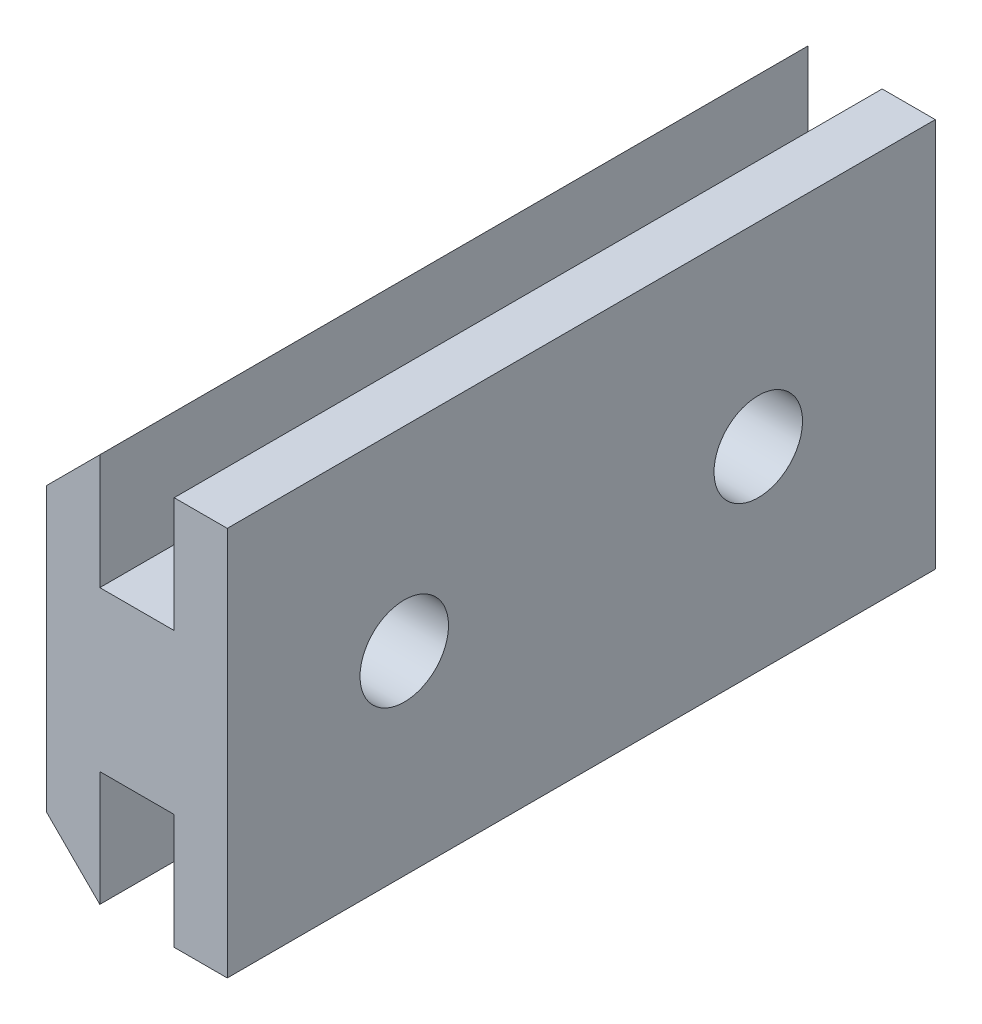
SolidWorks part; units mm, degrees
ref_plane "Plan de face" through (0, 0, 0) normal (0, 0, 1) x (1, 0, 0)
ref_plane "Plan de dessus" through (0, 0, 0) normal (0, 1, 0) x (1, 0, 0)
ref_plane "Plan de droite" through (0, 0, 0) normal (1, 0, 0) x (0, 0, -1)
sketch "ProfileRainureEsquisse" plane through (0, 0, 0) normal (0, 0, 1) x (1, 0, 0)
  line L0 (0.1, -1.75) -> (0.1, 6.25)
  line L1 (0.1, 6.25) -> (1.6, 7.75)
  line L2 (0.1, -1.75) -> (1.6, -3.25)
  line L3 (1.6, 7.75) -> (1.6, 4.5)
  line L4 (1.6, 4.5) -> (3.7, 4.5)
  line L5 (3.7, 4.5) -> (3.7, 7.75)
  line L6 (3.7, 0) -> (1.6, 0)
  line L7 (1.6, 0) -> (1.6, -3.25)
  line L8 (3.7, 7.75) -> (5.2, 7.75)
  line L9 (5.2, 7.75) -> (5.2, -3.25)
  line L10 (5.2, -3.25) -> (3.7, -3.25)
  line L11 (3.7, -3.25) -> (3.7, 0)
  dimension "D1" = 1.5
  dimension "D2" = 2.1
  dimension "D3" = 11
  dimension "D4" = 4.5
  dimension "D5" = 1.5
  dimension "D6" = 45
extrude "Boss.-Extru.1" add sketch "ProfileRainureEsquisse" along normal blind 20
sketch "Esquisse1" plane through (5.2, 0, 0) normal (1, 0, 0) x (0, 0, -1)
  line L0 (-20, -3.25) -> (-20, 7.75) construction
  line L1 (0, -3.25) -> (0, 7.75) construction
  circle A0 centre (-15, 2.25) radius 1.25
  circle A1 centre (-5, 2.25) radius 1.25
  point P2 (-20, 2.25)
  point P3 (0, 2.25)
  dimension "D1" = 2.5
  dimension "D3" = 2.5
  dimension "D2" = 5
  dimension "D4" = 5
extrude "Enlèv. mat.-Extru.1" cut sketch "Esquisse1" against normal through all
